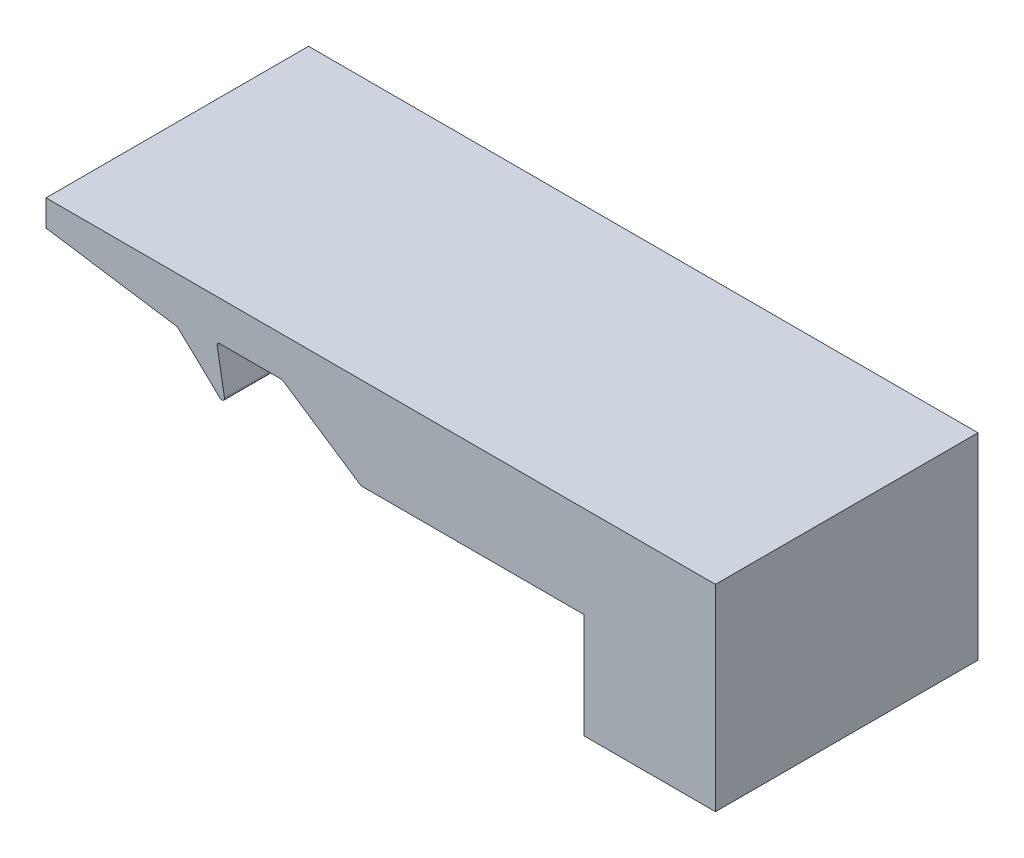
SolidWorks part; units mm, degrees
ref_plane "Front Plane" through (0, 0, 0) normal (0, 0, 1) x (1, 0, 0)
ref_plane "Top Plane" through (0, 0, 0) normal (0, 1, 0) x (1, 0, 0)
ref_plane "Right Plane" through (0, 0, 0) normal (1, 0, 0) x (0, 0, -1)
sketch "Sketch1" plane through (0, 0, 0) normal (0, 0, 1) x (1, 0, 0)
  line L8 (-17.6449, -3.0968) -> (-22.6449, -3.0968)
  line L9 (-22.6449, -3.0968) -> (-22.6449, 0.9032)
  line L12 (-36.2944, 0.9032) -> (-36.6449, 2.9032)
  line L14 (-43.1449, 3.4032) -> (-38.1449, 2.6532)
  line L16 (-22.6449, 0.9032) -> (-31.1449, 0.9032)
  line L17 (-31.1449, 0.9032) -> (-34.1449, 2.9032)
  line L23 (-34.1449, 2.9032) -> (-36.6449, 2.9032)
  line L25 (-38.1449, 2.6532) -> (-36.2944, 0.9032)
  line L30 (-43.1449, 4.4032) -> (-43.1449, 3.4032)
  line L43 (-43.1449, 4.4032) -> (-17.6449, 4.4032)
  line L44 (-17.6449, 4.4032) -> (-17.6449, -3.0968)
  dimension "D2" = 7.5
  dimension "D3" = 5
  dimension "D4" = 0.3505
  dimension "D5" = 1.75
  dimension "D6" = 1
  dimension "D7" = 5
  dimension "D8" = 3.5
  dimension "D9" = 1.5
  dimension "D10" = 14
  dimension "D11" = 16.5
  dimension "D12" = 13.5
  dimension "D13" = 25.5
  dimension "D14" = 18.6495
extrude "Boss-Extrude1" add sketch "Sketch1" along normal blind 10
fillet "Fillet1" radius 0.1 3 edges at (-36.2944, 0.9032, 5) (-34.1449, 2.9032, 5) (-36.6449, 2.9032, 5)
